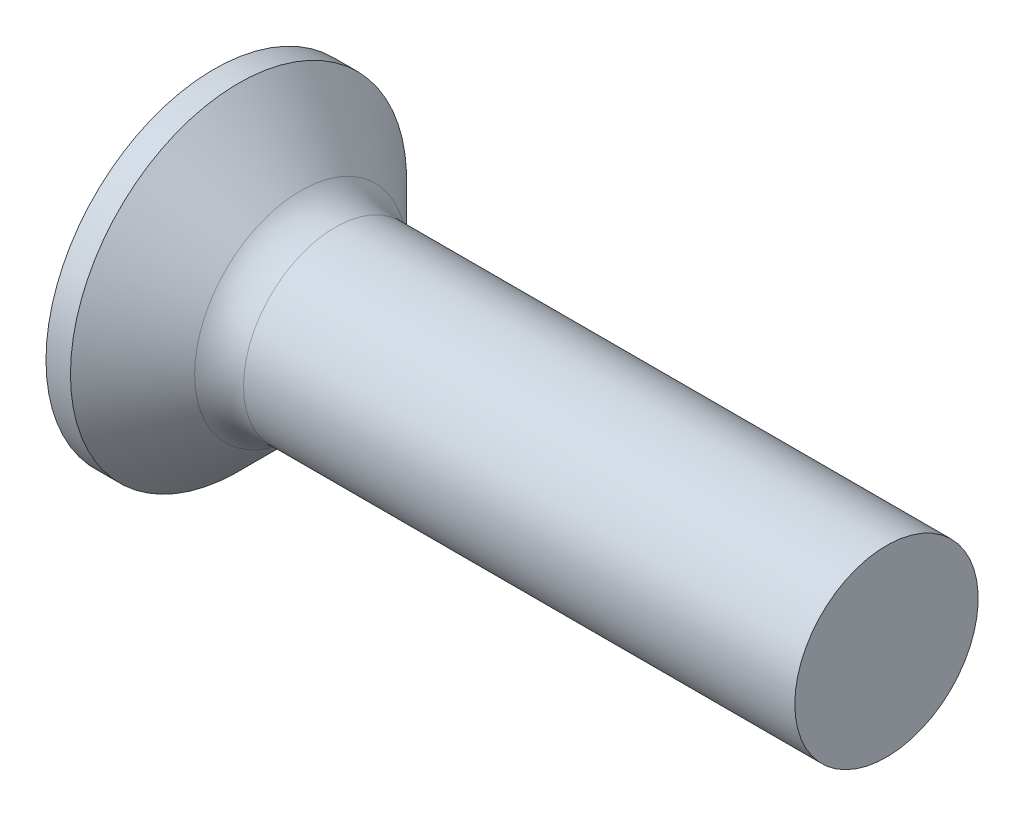
SolidWorks part; units mm, degrees
revolve "Base-Revolve" add sketch "BodySke"
sketch "BodySke" plane through (0, 0, 0) normal (0, 0, 1) x (1, 0, 0)
  line L0 (0, 0) -> (0, 2.75)
  line L1 (0, 2.75) -> (0.4, 2.75)
  line L2 (1.65, 1.5) -> (11, 1.5)
  line L3 (11, 1.5) -> (11, 0)
  line L4 (11, 0) -> (0, 0)
  line L5 (-6.35, 0) -> (82.55, 0) construction
  line L6 (1.65, -1.5) -> (11, -1.5) construction
  line L7 (0.4, -2.75) -> (1.65, -1.5) construction
  line L8 (0.4, 2.75) -> (1.65, 1.5)
  line L9 (0, -2.75) -> (0.4, -2.75) construction
  line L10 (2.15, 3.0875) -> (2.15, -6.4375) construction
  line L11 (7, 6.35) -> (7, -3.175) construction
  dimension "Diameter" = 3
  dimension "Length" = 11
  dimension "Head_ht" = 1.65
  dimension "Head_dia" = 5.5
  dimension "Head_ang" = 90
  dimension "D6" = 0.4
  dimension "Advance" = 0.5
  dimension "Thread_nom" = 4
cosmetic thread "ThreadCosmetic" [suppressed]
fillet "Fillet1" radius 0.8 1 edges at (1.65, 0, 1.5)
ref_plane "Plane1" through (0, 0, 0) normal (0, 0, 1) x (1, 0, 0)
ref_plane "Plane2" through (0, 0, 0) normal (0, 1, 0) x (1, 0, 0)
ref_plane "Plane3" through (0, 0, 0) normal (1, 0, 0) x (0, 0, -1)
sketch "Sketch3" plane through (0, 0, 0) normal (-1, 0, 0) x (0, 0, 1)
  line L0 (-0.37, 1.5) -> (0.37, 1.5)
  line L1 (0.37, 1.5) -> (0.37, -1.5)
  line L2 (0.37, -1.5) -> (-0.37, -1.5)
  line L3 (-0.37, -1.5) -> (-0.37, 1.5)
  dimension "Cross_dia" = 3
  dimension "Cross_width" = 0.74
  dimension "D1" = 1.5
  dimension "D2" = 0.37
ref_plane "Plane4" through (2.01, 0, 0) normal (-1, 0, 0) x (0, 0, 1)
sketch "Sketch4" plane through (2.01, 0, 0) normal (-1, 0, 0) x (0, 0, 1)
  line L0 (-0.37, 0.4979) -> (0.37, 0.4979)
  line L3 (0.37, 0.4979) -> (0.37, -0.4979)
  line L4 (0.37, -0.4979) -> (-0.37, -0.4979)
  line L5 (-0.37, -0.4979) -> (-0.37, 0.4979)
  dimension "D2" = 0.9957
  dimension "D1" = 0.74
  dimension "D4" = 0.4979
  dimension "D3" = 0.37
loft "Recess" cut profiles "Sketch3", "Sketch4"
pattern_circular "RecPat" count 2 every 90 about axis through (0, 0, 0) along (1, 0, 0) of "Recess"
sketch "RecCorSke" plane through (0, 0, 0) normal (0, 0, 1) x (1, 0, 0)
  line L0 (-3.175, 0) -> (15.875, 0) construction
  line L2 (0, 0) -> (0, 0.6966)
  line L3 (0, 0.6966) -> (2.01, 0.556)
  line L4 (2.01, 0.556) -> (2.1907, 0)
  line L5 (2.1907, 0) -> (0, 0)
  dimension "Diameter" = 1.112
  dimension "Depth" = 2.01
  dimension "Draft_angle" = 4
  dimension "Bottom_angle" = 18
revolve "RecessCore" cut sketch "RecCorSke" angle 360 about L0
sketch "ThdSchSke" plane through (0, 0, 0) normal (0, 0, 1) x (1, 0, 0)
  line L0 (7, -1.2195) -> (6.8036, -1.5)
  line L1 (7, -1.2195) -> (7.1964, -1.5)
  line L2 (7.1964, -1.5) -> (7.1964, -1.875)
  line L3 (-3.175, 0) -> (5.1513, 0) construction
  line L5 (7.1964, -1.875) -> (6.8036, -1.875)
  line L6 (6.8036, -1.875) -> (6.8036, -1.5)
  line L7 (0, 2.75) -> (0, -2.75) construction
  dimension "Diameter" = 3
  dimension "Thread_minor" = 2.439
  dimension "Start" = 7
revolve "ThreadSchematic" [suppressed] cut sketch "ThdSchSke" angle 360 about L3
pattern_linear "ThdSchPat" [suppressed]
equation "\"D1@Sketch3\" = \"Cross_dia@Sketch3\" / 2"
equation "\"D2@Sketch3\" = \"Cross_width@Sketch3\" / 2"
equation "\"Depth@RecCorSke\" = \"Cross_depth@Plane4\""
equation "\"D1@Sketch4\" = \"Cross_width@Sketch3\""
equation "\"D2@Sketch4\" = \"Cross_dia@Sketch3\" - 2.0 * \"Cross_depth@Plane4\" * tan(26.5  * 0.017453292)"
equation "\"D3@Sketch4\" = \"D1@Sketch4\" / 2"
equation "\"D4@Sketch4\" = \"D2@Sketch4\" / 2"
equation "\"Thread_length@ThreadCosmetic\" = ((sgn( (\"Length@BodySke\" - \"Advance@BodySke\" * 1.0 - \"Head_ht@BodySke\" ) - \"Thread_nom@BodySke\" )-1)*( (\"Length@BodySke\" - \"Advance@BodySke\" * 1.0 - \"Head_ht@BodySke\" ) - \"Thread_nom@BodySke\" ))/-2+ \"Thread_nom@BodySke\""
equation "\"Thread_minor@ThdSchSke\" = \"Thread_minor@ThreadCosmetic\""
equation "\"Diameter@ThdSchSke\" = \"Diameter@BodySke\""
equation "\"Overcut@ThdSchSke\" = \"Diameter@BodySke\" * 1.25"
equation "\"Start@ThdSchSke\" = 0.000001 + \"Length@BodySke\" - \"Thread_length@ThreadCosmetic\"  '---Countersunk---"
equation "\"Num_threads@ThdSchPat\" = int( \"Thread_length@ThreadCosmetic\" / \"Advance@BodySke\" + 0.999 )  + 1"
equation "\"Advance@ThdSchPat\" = \"Thread_length@ThreadCosmetic\" /  (\"Num_threads@ThdSchPat\" - 1) 'relax it"
